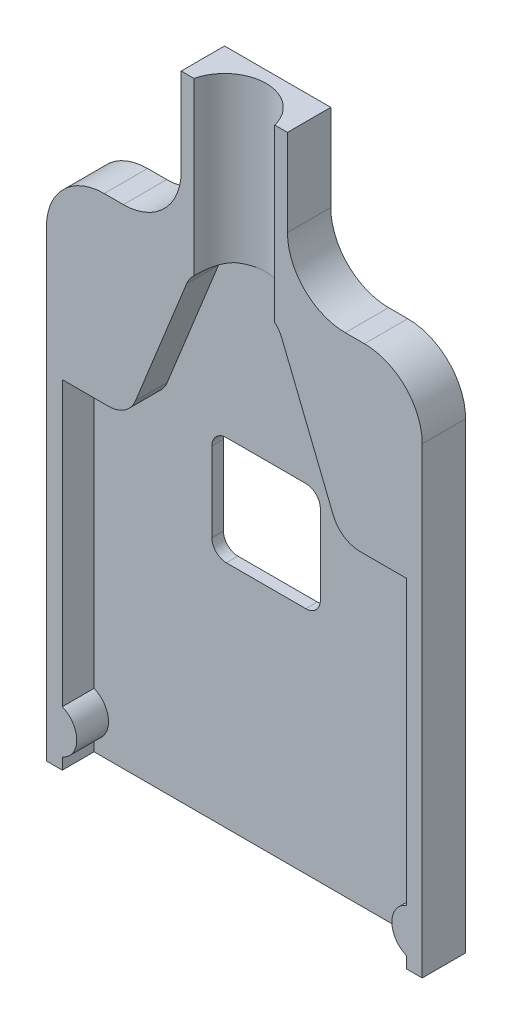
SolidWorks part; units mm, degrees
ref_plane "Front Plane" through (0, 0, 0) normal (0, 0, 1) x (1, 0, 0)
ref_plane "Top Plane" through (0, 0, 0) normal (0, 1, 0) x (1, 0, 0)
ref_plane "Right Plane" through (0, 0, 0) normal (1, 0, 0) x (0, 0, -1)
sketch "Sketch1" plane through (0, 0, 0) normal (0, 0, 1) x (1, 0, 0)
  line L0 (0, 36) -> (9.325, 36)
  line L1 (0, 0) -> (26, 0)
  line L2 (0, 0) -> (0, 36)
  line L4 (26, 0) -> (26, 36)
  line L5 (9.325, 36) -> (9.325, 46)
  line L6 (9.325, 46) -> (16.675, 46)
  line L7 (16.675, 46) -> (16.675, 36)
  line L8 (16.675, 36) -> (26, 36)
  line L9 (13, 0) -> (13, 46) construction
  point P11 (0, 0)
  point P12 (13, 46)
  dimension "D1" = 26
  dimension "D2" = 36
  dimension "D3" = 10
  dimension "D4" = 7.35
extrude "Boss-Extrude1" add sketch "Sketch1" along normal blind 3
sketch "Sketch2" plane through (0, 0, 3) normal (0, 0, 1) x (1, 0, 0)
  line L0 (1.5, 0) -> (1.5, 0.55) construction
  line L1 (0, 0) -> (26, 0) construction
  line L2 (1.5, 4.05) -> (1.5, 23) construction
  line L3 (1.5, 23) -> (24.5, 23) construction
  line L4 (13, 46) -> (13, 0) construction
  line L5 (16.675, 46) -> (9.325, 46) construction
  line L6 (1.5, 0) -> (24.5, 0) construction
  line L7 (24.5, 0) -> (24.5, 0.55) construction
  line L8 (24.5, 4.05) -> (24.5, 23) construction
  line L9 (1.1, -0.4) -> (1.1, 0.7958)
  line L10 (1.1, 3.8042) -> (1.1, 23.4)
  line L11 (1.1, 23.4) -> (24.9, 23.4)
  line L12 (24.9, 3.8042) -> (24.9, 23.4)
  line L13 (24.9, -0.4) -> (24.9, 0.7958)
  line L14 (1.1, -0.4) -> (24.9, -0.4)
  arc A0 (1.5, 4.05) -> (1.5, 0.55) centre (0.4688, 2.3) cw construction
  arc A1 (24.5, 4.05) -> (24.5, 0.55) centre (25.5313, 2.3) ccw construction
  arc A2 (1.1, 3.8042) -> (1.1, 0.7958) centre (0.4688, 2.3) cw
  arc A3 (24.9, 3.8042) -> (24.9, 0.7958) centre (25.5313, 2.3) ccw
  point P12 (2.5, 2.3)
  point P13 (2.545, 1.3837)
  point P14 (2.5782, 1.3837)
  point P20 (13, 23)
  dimension "D2" = 3.5
  dimension "D1" = 1
  dimension "D3" = 20.7
  dimension "D4" = 11.5
  dimension "D5" = 0.4
extrude "Cut-Extrude1" cut sketch "Sketch2" against normal offset from surface (2.2 mm away) 0.8 up to face at (13, 29.5, 0)
sketch "Sketch3" plane through (0, 46, 0) normal (0, 1, 0) x (1, 0, 0)
  line L0 (13, 0) -> (13, -3.675) construction
  line L1 (16.675, 0) -> (9.325, 0) construction
  circle A0 centre (13, -3.675) radius 2.875
  dimension "D1" = 3.675
extrude "Cut-Extrude2" cut sketch "Sketch3" against normal up to surface (22.6 mm away) up to face at (13, 23.4, 1.9)
sketch "Sketch4" plane through (0, 0, 3) normal (0, 0, 1) x (1, 0, 0)
  line L0 (5.6527, 23.4) -> (10.2054, 34.7)
  line L1 (10.2054, 23.4) -> (1.1, 23.4) construction
  line L2 (10.2054, 23.4) -> (10.2054, 46) construction
  line L3 (10.2054, 34.7) -> (15.7946, 34.7)
  line L4 (15.7946, 46) -> (15.7946, 23.4) construction
  line L5 (15.7946, 34.7) -> (20.3473, 23.4)
  line L6 (24.9, 23.4) -> (15.7946, 23.4) construction
  line L7 (20.3473, 23.4) -> (5.6527, 23.4)
extrude "Cut-Extrude3" cut sketch "Sketch4" against normal up to surface (2.2 mm away) up to face at (13, 8.8222, 0.8)
fillet "Fillet1" radius 2 4 edges at (15.7946, 34.7, 1.9) (10.2054, 34.7, 1.9) (20.3473, 23.4, 1.9) (5.6527, 23.4, 1.9)
fillet "Fillet2" radius 4 2 edges at (0, 36, 1.5) (26, 36, 1.5)
fillet "Fillet3" radius 4 2 edges at (9.325, 36, 1.5) (16.675, 36, 1.5)
sketch "Sketch5" plane through (0, 0, 0.8) normal (0, 0, 1) x (1, 0, 0)
  line L0 (1.1, 23.4) -> (24.9, 23.4) construction
  line L1 (9.25, 23.4) -> (16.75, 23.4)
  line L2 (9.25, 23.4) -> (9.25, 15.9)
  line L3 (9.25, 15.9) -> (16.75, 15.9)
  line L4 (16.75, 23.4) -> (16.75, 15.9)
  line L5 (1.1, 23.4) -> (1.1, 3.8042) construction
  line L6 (24.9, 3.8042) -> (24.9, 23.4) construction
  line L7 (4.3022, 23.4) -> (1.1, 23.4) construction
  point P10 (13, 23.4)
  point P11 (13, 23.4)
  dimension "D1" = 7.5
  dimension "D2" = 7.5
extrude "Cut-Extrude4" cut sketch "Sketch5" against normal up to surface (0.8 mm away) up to face at (13, 31.6667, 0)
fillet "Fillet4" radius 1 4 edges at (9.25, 15.9, 0.4) (16.75, 15.9, 0.4) (16.75, 23.4, 0.4) (9.25, 23.4, 0.4)
